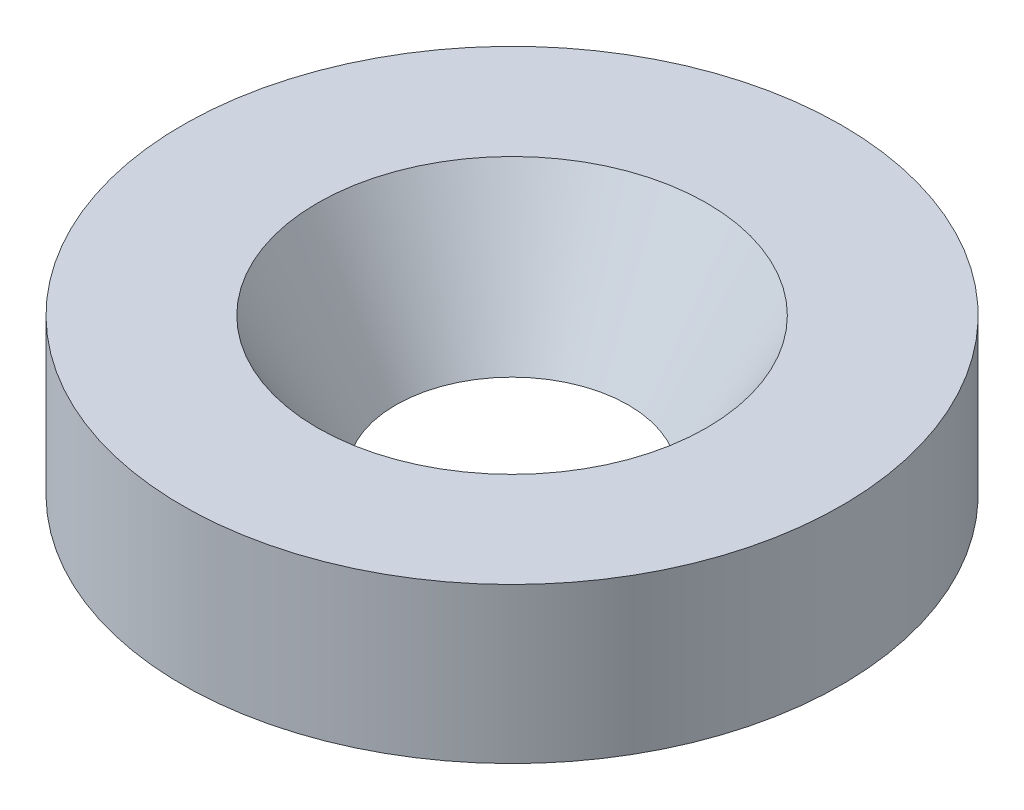
SolidWorks part; units mm, degrees
ref_plane "Front Plane" through (0, 0, 0) normal (0, 0, 1) x (1, 0, 0)
ref_plane "Top Plane" through (0, 0, 0) normal (0, 1, 0) x (1, 0, 0)
ref_plane "Right Plane" through (0, 0, 0) normal (1, 0, 0) x (0, 0, -1)
sketch "Sketch1" plane through (0, 0, 0) normal (1, 0, 0) x (0, 0, -1)
  line L0 (0, 0) -> (0, 8.891) construction
  line L1 (8, 0) -> (8.5, 0)
  line L2 (8.5, 0) -> (8.5, 4)
  line L3 (8.5, 4) -> (5.0207, 4)
  line L4 (5.0207, 4) -> (3, 0.5)
  line L5 (3, 0.5) -> (6, 0.5)
  line L6 (6, 0.5) -> (6, 2.75)
  line L7 (6, 2.75) -> (8, 2.75)
  line L8 (8, 2.75) -> (8, 0)
  point P5 (0, 0)
  dimension "D1" = 8.5
  dimension "D2" = 0.5
  dimension "D3" = 4
  dimension "D4" = 2
  dimension "D5" = 3
  dimension "D6" = 60
  dimension "D7" = 1.25
  dimension "D8" = 2.25
revolve "Revolve1" add sketch "Sketch1" angle 360 about L0
